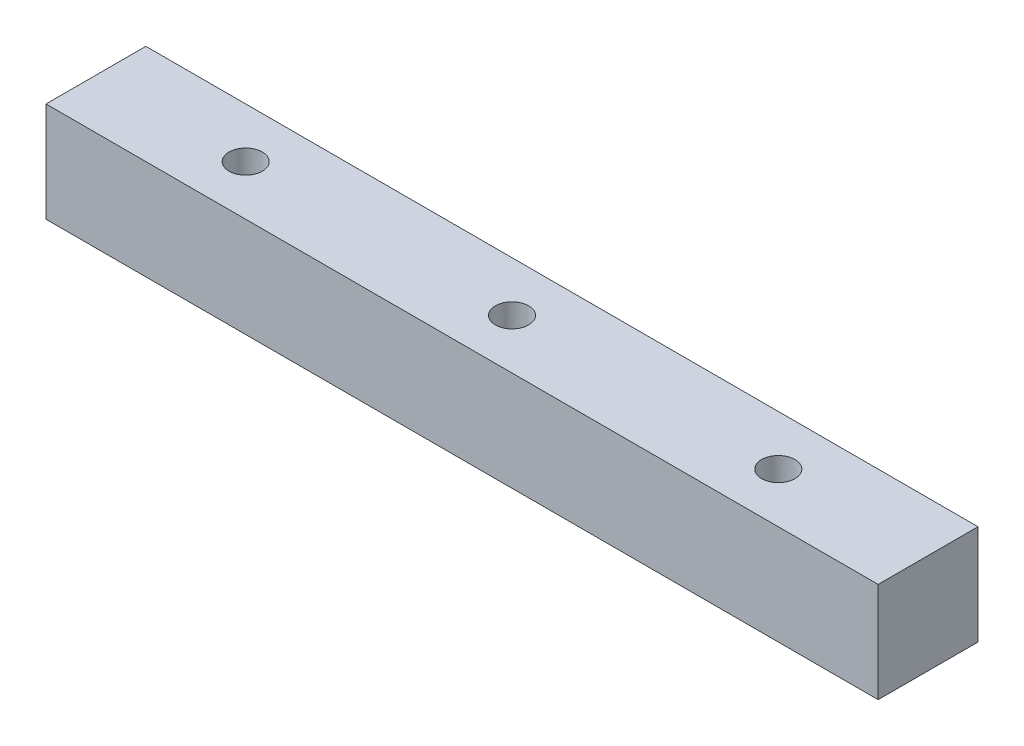
SolidWorks part; units mm, degrees
ref_plane "Front" through (0, 0, 0) normal (0, 0, 1) x (1, 0, 0)
ref_plane "Top" through (0, 0, 0) normal (0, 1, 0) x (1, 0, 0)
ref_plane "Right" through (0, 0, 0) normal (1, 0, 0) x (0, 0, -1)
sketch "草图1" plane through (0, 0, 0) normal (0, 1, 0) x (1, 0, 0)
  line L1 (12.5, -1.5) -> (-12.5, -1.5)
  line L2 (12.5, -1.5) -> (12.5, 1.5)
  line L3 (12.5, 1.5) -> (-12.5, 1.5)
  line L4 (-12.5, -1.5) -> (-12.5, 1.5)
  line L5 (12.5, -1.5) -> (-12.5, 1.5) construction
  line L6 (12.5, 1.5) -> (-12.5, -1.5) construction
  point P0 (0, 0)
  dimension "D1" = 3
  dimension "D2" = 25
extrude "凸台-拉伸1" add sketch "草图1" along normal blind 3
sketch "草图2" plane through (0, 3, 0) normal (0, 1, 0) x (1, 0, 0)
  line L0 (0, 0) -> (0, 7.7464) construction
  circle A0 centre (-8, 0) radius 0.5
  circle A1 centre (0, 0) radius 0.5
  circle A2 centre (8, 0) radius 0.5
  dimension "D2" = 1
  dimension "D3" = 1
  dimension "D1" = 16
extrude "切除-拉伸1" cut sketch "草图2" against normal through all
